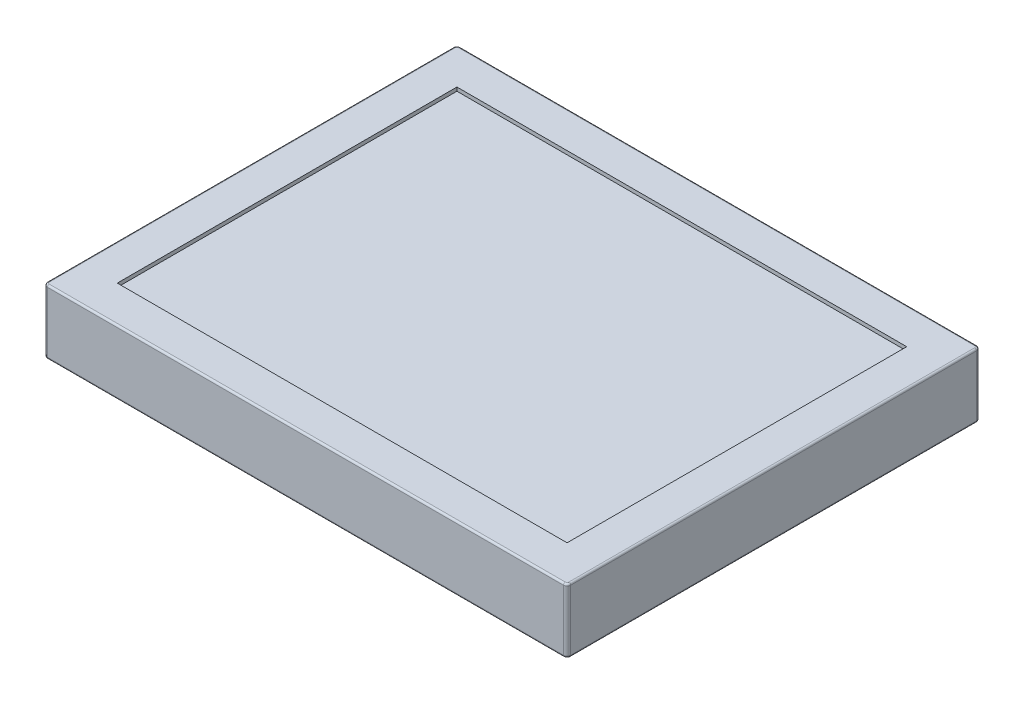
SolidWorks part; units mm, degrees
ref_plane "Front Plane" through (0, 0, 0) normal (0, 0, 1) x (1, 0, 0)
ref_plane "Top Plane" through (0, 0, 0) normal (0, 1, 0) x (1, 0, 0)
ref_plane "Right Plane" through (0, 0, 0) normal (1, 0, 0) x (0, 0, -1)
sketch "Sketch1" plane through (0, 0, 0) normal (0, 1, 0) x (1, 0, 0)
  line L1 (-142.5, 112.5) -> (142.5, 112.5)
  line L2 (-142.5, 112.5) -> (-142.5, -112.5)
  line L3 (-142.5, -112.5) -> (142.5, -112.5)
  line L4 (142.5, 112.5) -> (142.5, -112.5)
  line L5 (-142.5, 112.5) -> (142.5, -112.5) construction
  line L6 (-142.5, -112.5) -> (142.5, 112.5) construction
  point P0 (0, 0)
  dimension "D1" = 225
  dimension "D2" = 285
extrude "Boss-Extrude1" add sketch "Sketch1" along normal blind 35
sketch "Sketch2" plane through (0, 35, 0) normal (0, 1, 0) x (1, 0, 0)
  line L1 (-122.5, 92.5) -> (122.5, 92.5)
  line L2 (-122.5, 92.5) -> (-122.5, -92.5)
  line L3 (-122.5, -92.5) -> (122.5, -92.5)
  line L4 (122.5, 92.5) -> (122.5, -92.5)
  line L5 (-122.5, 92.5) -> (122.5, -92.5) construction
  line L6 (-122.5, -92.5) -> (122.5, 92.5) construction
  point P0 (0, 0)
extrude "Cut-Extrude1" cut sketch "Sketch2" against normal blind 2 contours L1 L4 L3 L2
fillet "Fillet1" radius 2 4 edges at (-142.5, 17.5, -112.5) (-142.5, 17.5, 112.5) (142.5, 17.5, -112.5) (142.5, 17.5, 112.5)
fillet "Fillet2" radius 1 8 edges at (141.9142, 35, 111.9142) (-141.9142, 35, 111.9142) (-141.9142, 35, -111.9142) (141.9142, 35, -111.9142) (-142.5, 35, 0) (0, 35, -112.5) (0, 35, 112.5) (142.5, 35, 0)
fillet "Fillet3" radius 1 8 edges at (141.9142, 0, 111.9142) (-141.9142, 0, 111.9142) (-141.9142, 0, -111.9142) (141.9142, 0, -111.9142) (0, 0, -112.5) (-142.5, 0, 0) (0, 0, 112.5) (142.5, 0, 0)
sketch "Sketch4" plane through (0, 0, 0) normal (0, -1, 0) x (1, 0, 0)
  line L0 (-140.5, -111.5) -> (140.5, -111.5) construction
  line L5 (-111.5, 111.5) -> (111.5, -111.5) construction
  line L6 (-111.5, -111.5) -> (111.5, 111.5) construction
  circle A0 centre (-24.7487, 24.7487) radius 2
  circle A1 centre (-35.3553, 35.3553) radius 2
  circle A2 centre (-45.9619, 45.9619) radius 2
  circle A3 centre (24.7487, 24.7487) radius 2
  circle A4 centre (35.3553, 35.3553) radius 2
  circle A5 centre (45.9619, 45.9619) radius 2
  circle A6 centre (24.7487, -24.7487) radius 2
  circle A7 centre (35.3553, -35.3553) radius 2
  circle A8 centre (45.9619, -45.9619) radius 2
  circle A9 centre (-24.7487, -24.7487) radius 2
  circle A10 centre (-35.3553, -35.3553) radius 2
  circle A11 centre (-45.9619, -45.9619) radius 2
  point P0 (0, 0)
  dimension "D2" = 4
  dimension "D3" = 4
  dimension "D4" = 4
  dimension "D14" = 4
  dimension "D15" = 4
  dimension "D16" = 4
  dimension "D17" = 4
  dimension "D18" = 4
  dimension "D19" = 4
  dimension "D23" = 4
  dimension "D24" = 4
  dimension "D25" = 4
  dimension "D1" = 223
  dimension "D5" = 35
  dimension "D6" = 15
  dimension "D7" = 15
  dimension "D8" = 35
  dimension "D9" = 15
  dimension "D10" = 15
  dimension "D11" = 35
  dimension "D12" = 15
  dimension "D13" = 15
  dimension "D20" = 15
  dimension "D21" = 15
  dimension "D22" = 35
extrude "Cut-Extrude2" cut sketch "Sketch4" against normal blind 2
